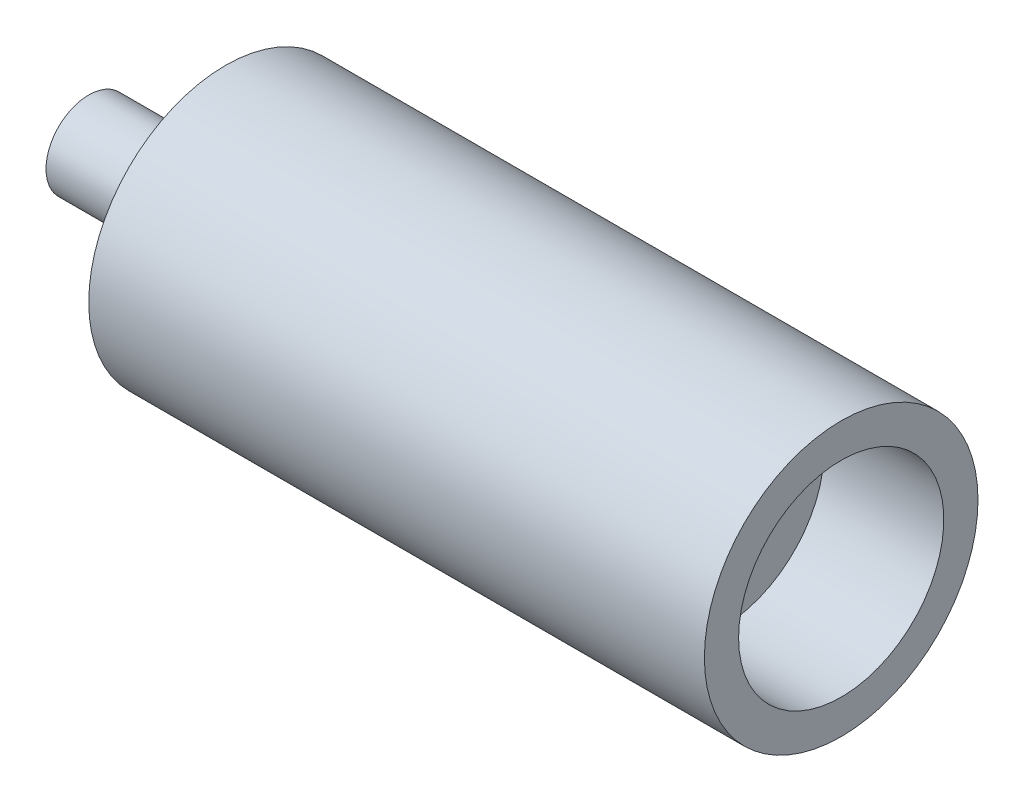
SolidWorks part; units mm, degrees
ref_plane "Front Plane" through (0, 0, 0) normal (0, 0, 1) x (1, 0, 0)
ref_plane "Top Plane" through (0, 0, 0) normal (0, 1, 0) x (1, 0, 0)
ref_plane "Right Plane" through (0, 0, 0) normal (1, 0, 0) x (0, 0, -1)
sketch "Sketch2" plane through (0, 0, 0) normal (0, 0, 1) x (1, 0, 0)
  line L0 (0, 0) -> (0, 12.5)
  line L1 (0, 12.5) -> (30, 12.5)
  line L2 (30, 12.5) -> (30, 20)
  line L3 (30, 20) -> (33, 25)
  line L4 (33, 25) -> (35, 25)
  line L5 (35, 25) -> (35, 32.5)
  line L6 (35, 32.5) -> (40, 32.5)
  line L7 (40, 32.5) -> (40, 40)
  line L8 (40, 40) -> (220, 40)
  line L9 (220, 40) -> (220, 30)
  line L10 (220, 30) -> (185, 30)
  line L11 (185, 30) -> (185, 0)
  line L12 (185, 0) -> (0, 0)
  line L13 (37.7601, 0) -> (65.321, 0) construction
  dimension "D1" = 80
  dimension "D2" = 10
  dimension "D3" = 25
  dimension "D4" = 30
  dimension "D5" = 50
  dimension "D6" = 40
  dimension "D7" = 35
  dimension "D8" = 2
  dimension "D9" = 65
  dimension "D10" = 5
  dimension "D11" = 180
  dimension "D12" = 35
revolve "Revolve1" add sketch "Sketch2" angle 360 about L13
